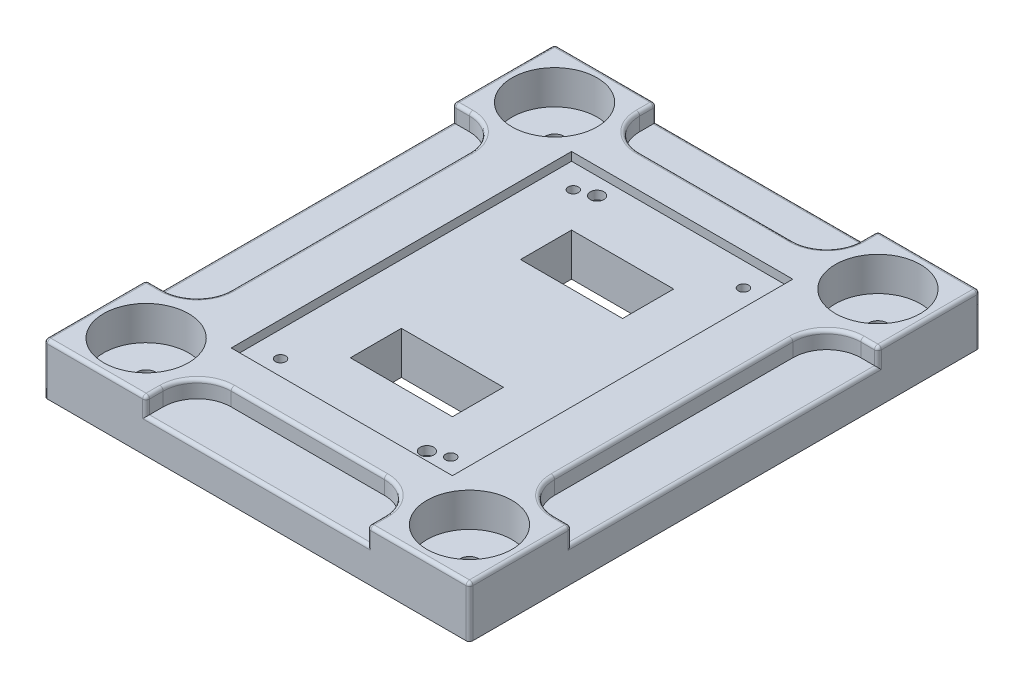
SolidWorks part; units mm, degrees
material "1060 Alloy"
ref_plane "Front Plane" through (0, 0, 0) normal (0, 0, 1) x (1, 0, 0)
ref_plane "Top Plane" through (0, 0, 0) normal (0, 1, 0) x (1, 0, 0)
ref_plane "Right Plane" through (0, 0, 0) normal (1, 0, 0) x (0, 0, -1)
sketch "Sketch1" plane through (0, 0, 0) normal (0, 1, 0) x (1, 0, 0)
  line L7 (-125, 150) -> (125, 150)
  line L8 (-125, 150) -> (-125, -150)
  line L9 (-125, -150) -> (125, -150)
  line L10 (125, 150) -> (125, -150)
  line L11 (-125, 150) -> (125, -150) construction
  line L12 (-125, -150) -> (125, 150) construction
  point P0 (0, 0)
  point P6 (0, 0)
  dimension "D3" = 250
  dimension "D4" = 300
extrude "Boss-Extrude1" add sketch "Sketch1" along normal blind 30
sketch "Sketch2" plane through (0, 30, 0) normal (0, 1, 0) x (1, 0, 0)
  line L0 (-30, 65) -> (30, 65)
  line L1 (-30, 65) -> (-30, 35)
  line L2 (-30, 35) -> (30, 35)
  line L3 (30, 65) -> (30, 35)
  line L4 (-30, -35) -> (30, -35)
  line L9 (0, 50) -> (50000, 50) construction
  line L10 (0, -50) -> (50000, -50) construction
  line L11 (-30, -35) -> (-30, -65)
  line L12 (-30, -65) -> (30, -65)
  line L13 (30, -35) -> (30, -65)
  line L14 (0, 0) -> (0, -50000) construction
  point P4 (0, 0)
  dimension "D1" = 60
  dimension "D2" = 30
  dimension "D3" = 50
  dimension "D4" = 50
  dimension "D6" = 60
  dimension "D7" = 30
extrude "Cut-Extrude1" cut sketch "Sketch2" against normal blind 246
sketch "Sketch4" plane through (0, 30, 0) normal (0, 1, 0) x (1, 0, 0)
  line L1 (-65, 100) -> (65, 100)
  line L2 (-65, 100) -> (-65, -100)
  line L3 (-65, -100) -> (65, -100)
  line L4 (65, 100) -> (65, -100)
  line L5 (-65, 100) -> (65, -100) construction
  line L6 (-65, -100) -> (65, 100) construction
  point P0 (0, 0)
  dimension "D1" = 200
  dimension "D2" = 130
extrude "Cut-Extrude2" cut sketch "Sketch4" against normal blind 5
hole_wizard "CBORE for M5 Hex Socket Head Cap Screw1" positions "3DSketch2" profile "Sketch7" counterbore size "M5" standard "ISO"
sketch3d "3DSketch2"
  line L11 (0, 0, 0) -> (0, 0, -50000) construction
  line L12 (0, 0, 0) -> (50000, 0, 0) construction
  point P0 (50, 0, -86)
  point P2 (-50, 0, -86)
  point P4 (-50, 0, 86)
  point P6 (50, 0, 86)
  dimension "D1" = 50
  dimension "D2" = 86
  dimension "D3" = 86
  dimension "D5" = 86
  dimension "D4" = 86
  dimension "D6" = 50
  dimension "D7" = 50
  dimension "D8" = 50
sketch "Sketch7" plane through (50, 0, -86) normal (1, 0, 0) x (0, 0, -1)
  line L0 (0, 0) -> (0, 31.8026)
  line L1 (0, 31.8026) -> (3, 30)
  line L2 (3, 30) -> (3, 6)
  line L3 (3, 6) -> (4, 6)
  line L4 (4, 6) -> (4, 0)
  line L5 (4, 0) -> (0, 0)
  line L10 (0, 31.8026) -> (-3, 30) construction
  line L11 (0, -6.35) -> (0, 107.95) construction
  dimension "Hole Dia." = 6
  dimension "Hole Depth" = 30
  dimension "C'Bore Dia." = 8
  dimension "C'Bore Depth" = 6
  dimension "Drill Angle" = 118
sketch "Sketch10" plane through (0, 30, 0) normal (0, 1, 0) x (1, 0, 0)
  line L0 (-125, 150) -> (-125, -150) construction
  line L1 (-125, 90) -> (-115, 90)
  line L2 (-125, 90) -> (-125, -90)
  line L3 (-125, -90) -> (-115, -90)
  line L4 (-95, 70) -> (-95, -70)
  line L5 (-125, -150) -> (125, -150) construction
  line L6 (-65, -150) -> (65, -150)
  line L7 (-65, -150) -> (-65, -140)
  line L8 (-45, -120) -> (45, -120)
  line L9 (65, -150) -> (65, -140)
  line L10 (125, -150) -> (125, 150) construction
  line L11 (125, -90) -> (115, -90)
  line L12 (125, -90) -> (125, 90)
  line L13 (125, 90) -> (115, 90)
  line L14 (95, -70) -> (95, 70)
  line L15 (125, 150) -> (-125, 150) construction
  line L16 (65, 150) -> (-65, 150)
  line L17 (65, 150) -> (65, 140)
  line L18 (45, 120) -> (-45, 120)
  line L19 (-65, 150) -> (-65, 140)
  arc A0 (-95, -70) -> (-115, -90) centre (-115, -70) cw
  arc A1 (-95, 70) -> (-115, 90) centre (-115, 70) ccw
  arc A2 (-45, 120) -> (-65, 140) centre (-45, 140) cw
  arc A3 (45, 120) -> (65, 140) centre (45, 140) ccw
  arc A4 (95, 70) -> (115, 90) centre (115, 70) cw
  arc A5 (45, -120) -> (65, -140) centre (45, -140) cw
  arc A6 (-65, -140) -> (-45, -120) centre (-45, -140) cw
  arc A7 (95, -70) -> (115, -90) centre (115, -70) ccw
  point P30 (-65, 120)
  point P35 (95, 90)
  dimension "D13" = 20
  dimension "D14" = 20
  dimension "D15" = 20
  dimension "D16" = 20
  dimension "D17" = 20
  dimension "D18" = 20
  dimension "D19" = 20
  dimension "D20" = 20
  dimension "D1" = 30
  dimension "D2" = 60
  dimension "D3" = 60
  dimension "D4" = 30
  dimension "D5" = 60
  dimension "D6" = 60
  dimension "D7" = 60
  dimension "D8" = 60
  dimension "D9" = 60
  dimension "D10" = 60
  dimension "D11" = 30
  dimension "D12" = 30
extrude "Cut-Extrude4" cut sketch "Sketch10" against normal blind 10
fillet "Fillet1" radius 2 5 edges at (65, 30, 145) (59.1421, 30, 125.8579) (0, 30, 120) (-65, 30, 145) (-59.1421, 30, 125.8579)
fillet "Fillet2" radius 2 3 edges at (-65, 24, 150) (-65.5858, 29.4142, 150) (-96, 30, 150)
fillet "Fillet3" radius 2 3 edges at (65, 24, 150) (65.5858, 29.4142, 150) (96, 30, 150)
fillet "Fillet4" radius 2 3 edges at (125, 14, 150) (125, 29.4142, 149.4142) (125, 30, 119)
fillet "Fillet5" radius 2 7 edges at (125, 24, 90) (124.4142, 29.4142, 90) (119, 30, 90) (120, 30, -90) (100.8579, 30, -84.1421) (95, 30, 0) (100.8579, 30, 84.1421)
fillet "Fillet7" radius 2 3 edges at (125, 24, -90) (125, 29.4142, -90.5858) (125, 30, -121)
fillet "Fillet8" radius 2 5 edges at (-65, 30, -145) (-59.1421, 30, -125.8579) (0, 30, -120) (65, 30, -145) (59.1421, 30, -125.8579)
fillet "Fillet9" radius 2 5 edges at (125, 14, -150) (124.4142, 29.4142, -150) (65, 24, -150) (65.5858, 29.4142, -150) (95, 30, -150)
fillet "Fillet10" radius 2 3 edges at (-65, 24, -150) (-65.5858, 29.4142, -150) (-96, 30, -150)
fillet "Fillet11" radius 2 3 edges at (-125, 14, -150) (-125, 29.4142, -149.4142) (-125, 30, -119)
fillet "Fillet12" radius 2 7 edges at (-120, 30, 90) (-100.8579, 30, 84.1421) (-95, 30, 0) (-125, 24, -90) (-124.4142, 29.4142, -90) (-119, 30, -90) (-100.8579, 30, -84.1421)
fillet "Fillet13" radius 2 5 edges at (-125, 24, 90) (-125, 29.4142, 90.5858) (-125, 14, 150) (-125, 29.4142, 149.4142) (-125, 30, 120)
fillet "Fillet14" radius 2 1 edges at (-125, 20, 0)
fillet "Fillet15" radius 2 1 edges at (0, 20, 150)
fillet "Fillet16" radius 2 1 edges at (125, 20, 0)
fillet "Fillet17" radius 2 1 edges at (0, 20, -150)
sketch "Sketch11" plane through (0, 30, 0) normal (0, 1, 0) x (1, 0, 0)
  line L0 (0, 0) -> (0, -50000) construction
  line L1 (0, 0) -> (50000, 0) construction
  circle A0 centre (-95, 120) radius 25
  circle A1 centre (95, 120) radius 25
  circle A2 centre (95, -120) radius 25
  circle A3 centre (-95, -120) radius 25
  dimension "D1" = 50
  dimension "D2" = 95
  dimension "D3" = 120
extrude "Cut-Extrude5" cut sketch "Sketch11" against normal blind 20
sketch "Sketch12" plane through (0, 0, 0) normal (0, -1, 0) x (1, 0, 0)
  line L0 (0, 0) -> (0, -50000) construction
  line L1 (0, 0) -> (50000, 0) construction
hole_wizard "CBORE for M5 Hex Head Bolt3" positions "3DSketch4" profile "Sketch17" counterbore size "M5" standard "ISO" end condition through all
sketch3d "3DSketch4"
  line L0 (0, 0, 0) -> (0, 0, -50000) construction
  line L1 (0, 0, 0) -> (50000, 0, 0) construction
  point P0 (95, 0, -120)
  point P2 (-95, 0, -120)
  point P4 (-95, 0, 120)
  point P6 (95, 0, 120)
  dimension "D1" = 95
  dimension "D2" = 120
  dimension "D3" = 95
  dimension "D4" = 120
  dimension "D5" = 120
  dimension "D6" = 95
  dimension "D7" = 95
  dimension "D8" = 120
sketch "Sketch17" plane through (95, 0, -120) normal (1, 0, 0) x (0, 0, -1)
  line L0 (0, 0) -> (0, 30)
  line L1 (0, 30) -> (5.5, 30)
  line L3 (5.5, 30) -> (5.5, 8)
  line L4 (5.5, 8) -> (8, 8)
  line L5 (8, 8) -> (8, 0)
  line L7 (8, 0) -> (0, 0)
  line L11 (0, -6.35) -> (0, 107.95) construction
  dimension "Thru Hole Dia." = 11
  dimension "Thru Hole Depth" = 30
  dimension "C'Bore Dia." = 16
  dimension "C'Bore Depth" = 8
sketch "Sketch26" plane through (0, 25, 0) normal (0, 1, 0) x (1, 0, 0)
  line L0 (0, 0) -> (0, -50000) construction
  line L1 (0, 0) -> (50000, 0) construction
  line L2 (65, 100) -> (-65, 100) construction
  line L3 (-65, -100) -> (65, -100) construction
  circle A0 centre (40, -90) radius 4
  circle A1 centre (-40, 90) radius 4
  dimension "D1" = 8
  dimension "D2" = 8
  dimension "D3" = 40
  dimension "D4" = 40
  dimension "D5" = 10
  dimension "D6" = 10
extrude "Cut-Extrude6" cut sketch "Sketch26" against normal blind 5
